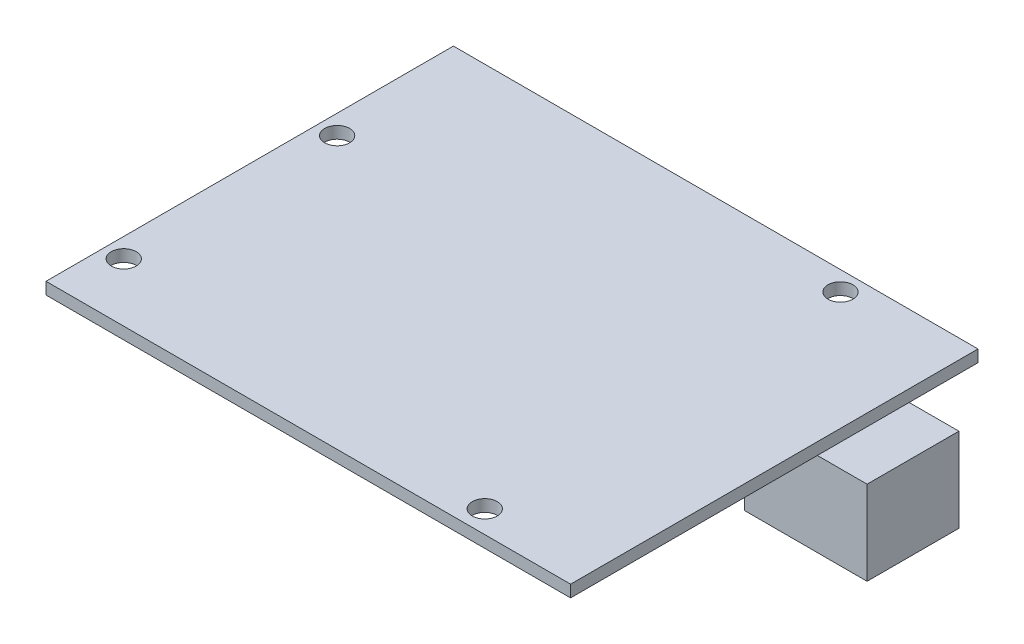
SolidWorks part; units mm, degrees
ref_plane "Front Plane" through (0, 0, 0) normal (0, 0, 1) x (1, 0, 0)
ref_plane "Top Plane" through (0, 0, 0) normal (0, 1, 0) x (1, 0, 0)
ref_plane "Right Plane" through (0, 0, 0) normal (1, 0, 0) x (0, 0, -1)
sketch "Sketch1" plane through (0, 0, 0) normal (0, 1, 0) x (1, 0, 0)
  line L7 (66.04, 45.64) -> (-2.54, 45.64)
  line L8 (66.04, 45.64) -> (66.04, -7.62)
  line L9 (66.04, -7.62) -> (-2.54, -7.62)
  line L10 (-2.54, 45.64) -> (-2.54, -7.62)
  line L11 (66.04, 45.64) -> (-2.54, -7.62) construction
  line L12 (66.04, -7.62) -> (-2.54, 45.64) construction
  circle A0 centre (0, 0) radius 1.632
  circle A1 centre (0, 27.9) radius 1.632
  circle A2 centre (51.9, -4.7) radius 1.6319
  circle A3 centre (50.6, 43.1) radius 1.6319
  point P6 (66.7827, -8.4973)
  point P9 (0, 0)
  point P10 (31.75, 19.01)
  dimension "D2" = 3.2639
  dimension "D1" = 27.9
  dimension "D3" = 4.7
  dimension "D4" = 51.9
  dimension "D5" = 50.6
  dimension "D6" = 53.26
  dimension "D9" = 68.58
  dimension "D10" = 2.54
  dimension "D11" = 7.62
  dimension "D12" = 2.54
extrude "Boss-Extrude1" add sketch "Sketch1" along normal blind 1.56
sketch "Sketch2" plane through (0, 0, 0) normal (0, -1, 0) x (-1, 0, 0)
  line L0 (-66.04, 45.64) -> (2.54, 45.64) construction
  line L1 (-56.54, 24.64) -> (-72.54, 24.64)
  line L2 (-56.54, 24.64) -> (-56.54, 36.64)
  line L3 (-56.54, 36.64) -> (-72.54, 36.64)
  line L4 (-72.54, 24.64) -> (-72.54, 36.64)
  line L5 (-56.54, 24.64) -> (-72.54, 36.64) construction
  line L6 (-56.54, 36.64) -> (-72.54, 24.64) construction
  line L7 (-66.04, -7.62) -> (-66.04, 45.64) construction
  point P0 (-64.54, 30.64)
  dimension "D1" = 15
  dimension "D2" = 16
  dimension "D3" = 12
  dimension "D4" = 6.5
extrude "Boss-Extrude2" add sketch "Sketch2" along normal blind 11
